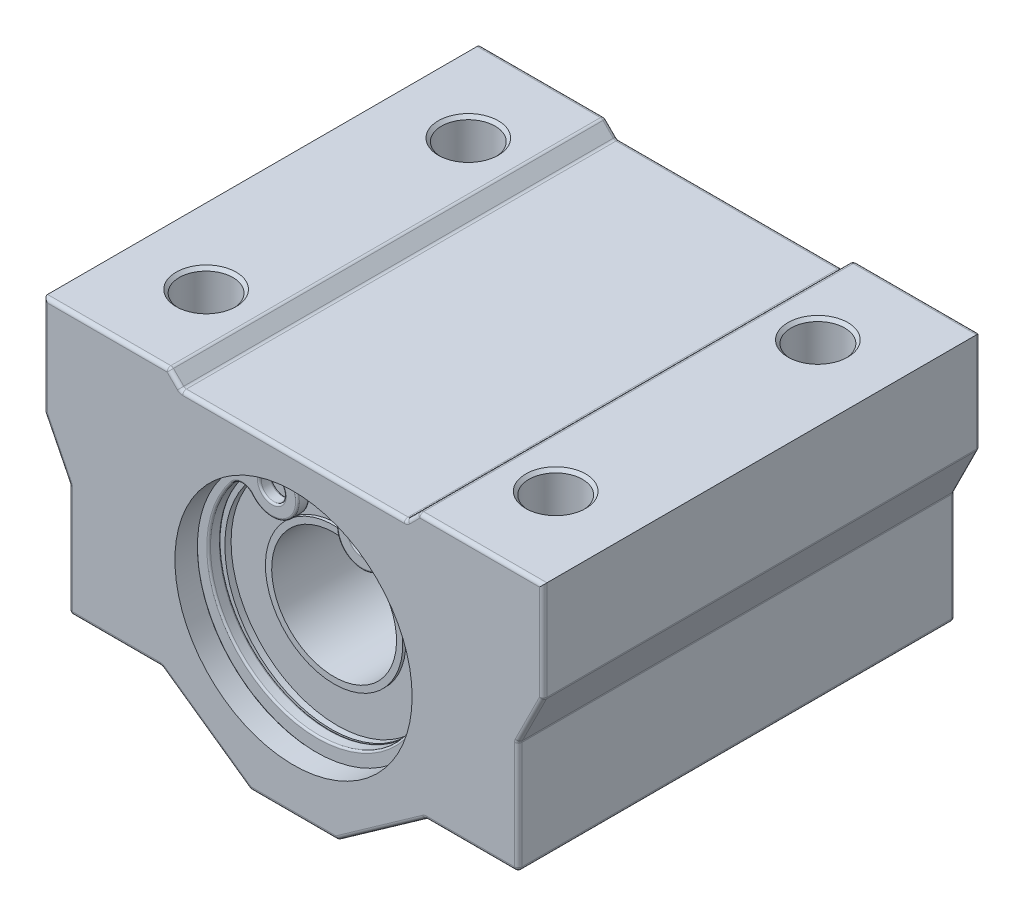
SolidWorks part; units mm, degrees
material "6061 Alloy"
ref_plane "Piano frontale" through (0, 0, 0) normal (0, 0, 1) x (1, 0, 0)
ref_plane "Piano superiore" through (0, 0, 0) normal (0, 1, 0) x (1, 0, 0)
ref_plane "Piano destro" through (0, 0, 0) normal (1, 0, 0) x (0, 0, -1)
sketch "Schizzo1" plane through (0, 0, 0) normal (0, 0, 1) x (1, 0, 0)
  line L0 (0, 25) -> (0, -25) construction
  line L1 (-30, 0) -> (30, 0) construction
  line L2 (3.5, -13) -> (10.5833, -8)
  line L3 (10.5833, -8) -> (18, -8)
  line L4 (18, -8) -> (18, 1)
  line L5 (18, 1) -> (20, 5)
  line L6 (20, 5) -> (20, 13)
  line L8 (20, 13) -> (10, 13)
  line L9 (9, 12) -> (10, 13)
  line L10 (-20, 12) -> (19, 12) construction
  line L15 (-3.5, -13) -> (-10.5833, -8)
  line L16 (-10.5833, -8) -> (-18, -8)
  line L17 (-18, -8) -> (-18, 1)
  line L18 (-18, 1) -> (-20, 5)
  line L19 (-20, 5) -> (-20, 13)
  line L20 (-20, 13) -> (-10, 13)
  line L24 (-9, 12) -> (-10, 13)
  line L26 (-9, 12) -> (9, 12)
  line L27 (-3.5, -13) -> (3.5, -13)
  circle A0 centre (0, 0) radius 9.5
  point P3 (0, 0)
  point P6 (0, 0)
  point P8 (0, -13)
  point P17 (0, 12)
  point P24 (19.5, 12.5)
  point P55 (0, -7.6504)
  dimension "D4" = 19
  dimension "D5" = 7
  dimension "D2" = 9
  dimension "D1" = 45
  dimension "D3" = 35.218
  dimension "D6" = 1
  dimension "D8" = 36
  dimension "G" = 21
  dimension "T" = 8
  dimension "F" = 26
  dimension "W" = 40
  dimension "E" = 20
  dimension "h" = 13
  dimension "L1" = 12
extrude "Estrusione-Estrusione1" add sketch "Schizzo1" along normal mid plane 35
hole_wizard "Foro per Vite M5-2" positions "Schizzo3" profile "Schizzo4" hole size "M5" standard "ISO" end condition through all
sketch "Schizzo3" plane through (0, 13, 0) normal (0, 1, 0) x (1, 0, 0)
  line L3 (0, 0) -> (-18, 0) construction
  line L5 (0, 0) -> (0, 17) construction
  line L6 (-20, -17.5) -> (-20, 17.5) construction
  line L7 (-10, 17.5) -> (-20, 17.5) construction
  point P0 (-14, 10.5)
  dimension "D1" = 14
  dimension "D2" = 10.5
  dimension "D3" = 6
  dimension "D4" = 7
sketch "Schizzo4" plane through (-14, 13, -10.5) normal (1, 0, 0) x (0, 0, 1)
  line L0 (0, 0) -> (0, 26)
  line L1 (0, 26) -> (2.15, 26)
  line L2 (2.15, 26) -> (2.15, 0)
  line L5 (2.15, 0) -> (0, 0)
  line L11 (0, -6.35) -> (0, 107.95) construction
  dimension "Thru Hole Dia." = 4.3
  dimension "Thru Hole Depth" = 26
pattern_linear "Ripetizione a L1" count 2 spacing 28 along (1, 0, 0) count 2 spacing 21 along (0, 0, 1) of "Foro per Vite M5-2"
chamfer "Smusso1" distance 0.25 angle 45 4 edges at (-14, 13, 12.65) (14, 13, 12.65) (14, 13, -8.35) (-14, 13, -8.35)
chamfer "Smusso2" distance 0.5 angle 45 4 edges at (14, -8, -8.35) (14, -8, 12.65) (-16.15, -8, 10.5) (-16.15, -8, -10.5)
sketch "Schizzo6" plane through (0, 0, 0) normal (1, 0, 0) x (0, 0, -1)
  line L0 (-20, 0) -> (20, 0) construction
  line L3 (-14.5, 8.5) -> (-14, 8.5)
  line L4 (-14, 8.5) -> (-14, 5.5)
  line L9 (14, 8.5) -> (14, 5.5)
  line L13 (-14.5, 9.5) -> (-14.5, 8.5)
  line L14 (0, -1.396) -> (0, 15.3751) construction
  line L15 (-14.5, 9.5) -> (14.5, 9.5)
  line L18 (14.5, 9.5) -> (14.5, 8.5)
  line L19 (14.5, 8.5) -> (14, 8.5)
  line L20 (-14, 5.5) -> (-14.25, 5.5)
  line L21 (14, 5.5) -> (14.25, 5.5)
  line L22 (-14.25, 5.5) -> (-14.25, 0)
  line L23 (14.25, 5.5) -> (14.25, 0)
  line L24 (14.25, 0) -> (-14.25, 0)
  point P3 (0, 0)
  point P7 (0, 9.5)
  dimension "D1" = 29
  dimension "D2" = 1
  dimension "D3" = 0.5
  dimension "D4" = 0.25
  dimension "D5" = 5.5
  dimension "D6" = 9.5
revolve "Rivoluzione1" add sketch "Schizzo6" angle 360 about L0
fillet "Raccordo1" radius 0.3 46 edges at (-10, 13, 0) (-9, 12, 0) (10, 13, 0) (9, 12, 0) (-20, 5, 0) (-18, 1, 0) (-18, -8, 0) (-10.5833, -8, 0) (20, 5, 0) (18, -8, 0) (18, 1, 0) (10.5833, -8, 0) (-3.5, -13, 0) (3.5, -13, 0) (-7.0417, -10.5, 17.5) (-14.2917, -8, 17.5) (-18, -3.5, 17.5) (-19, 3, 17.5) (-20, 9, 17.5) (-15, 13, 17.5) (-9.5, 12.5, 17.5) (0, 12, 17.5) (9.5, 12.5, 17.5) (15, 13, 17.5) (20, 9, 17.5) (19, 3, 17.5) (18, -3.5, 17.5) (14.2917, -8, 17.5) (7.0417, -10.5, 17.5) (0, -13, 17.5) (7.0417, -10.5, -17.5) (14.2917, -8, -17.5) (18, -3.5, -17.5) (19, 3, -17.5) (20, 9, -17.5) (15, 13, -17.5) (9.5, 12.5, -17.5) (0, 12, -17.5) (-9.5, 12.5, -17.5) (-15, 13, -17.5) (-20, 9, -17.5) (-19, 3, -17.5) (-18, -3.5, -17.5) (-14.2917, -8, -17.5) (-7.0417, -10.5, -17.5) (0, -13, -17.5)
sketch "Schizzo8" plane through (0, 0, 0) normal (0, 0, 1) x (1, 0, 0)
  circle A0 centre (0, 0) radius 5
  dimension "D1" = 10
extrude "Taglio-Estrusione2" cut sketch "Schizzo8" against normal through all both and the other way through all
sketch "Schizzo7" plane through (0, 0, 0) normal (0, 0, 1) x (1, 0, 0)
  circle A0 centre (0, 0) radius 10
  dimension "D1" = 20
extrude "Taglio-Estrusione1" cut sketch "Schizzo7" along normal blind 1.1 from offset 14.6
mirror "Specchia1" about plane through (0, 0, 0) normal (0, 0, 1) of "Taglio-Estrusione1"
sketch "Schizzo9" plane through (0, 0, 0) normal (0, 0, 1) x (1, 0, 0)
  line L0 (-2.0925, 0) -> (2.1999, 0) construction
  line L1 (0, 22.577) -> (0, -2.423) construction
  line L2 (0, 0) -> (10.9663, 21.9949) construction
  line L3 (0, 0) -> (-11.179, 22.4215) construction
  arc A0 (-3.9648, 8.9075) -> (4.0283, 8.8789) centre (0, 0) ccw
  circle A2 centre (-3.6325, 6.9465) radius 1
  circle A3 centre (3.5909, 6.9185) radius 1
  arc A4 (-5.2379, 5.6717) -> (-3.4873, 8.9914) centre (-3.6325, 6.9465) ccw
  arc A5 (3.6382, 8.968) -> (5.2175, 5.6709) centre (3.5909, 6.9185) ccw
  arc A6 (-6.8029, 5.6731) -> (6.7917, 5.6872) centre (0, 0.25) ccw
  arc A7 (3.6382, 8.968) -> (4.0283, 8.8789) centre (3.6151, 7.9683) cw
  arc A8 (-3.9648, 8.9075) -> (-3.4873, 8.9914) centre (-3.5581, 7.9939) cw
  arc A9 (5.2175, 5.6709) -> (6.7917, 5.6872) centre (6.011, 5.0623) cw
  arc A10 (-5.2379, 5.6717) -> (-6.8029, 5.6731) centre (-6.021, 5.0498) ccw
  dimension "D1" = 19.5
  dimension "D3" = 0.25
  dimension "D6" = 2.05
  dimension "D5" = 8.7
  dimension "D7" = 2
  dimension "D4" = 53
  dimension "D8" = 26.5
extrude "Estrusione-Estrusione2" add sketch "Schizzo9" along normal blind 1 from offset 14.6 separate body
pattern_linear "Ripetizione a L2" count 2 spacing 30.2 along (0, 0, -1) of "Estrusione-Estrusione2"
fillet "Raccordo4" radius 0.15 20 edges at (4.5909, 6.9185, 15.6) (-2.6325, 6.9465, 14.6) (-2.6325, 6.9465, 15.6) (3.8377, 8.9432, 14.6) (1.7421, 6.0329, 14.6) (6.0006, 6.0622, 14.6) (-6.0201, 6.0498, 14.6) (-1.8192, 5.9903, 14.6) (-3.7312, 8.9788, 14.6) (-0.0348, -9.7499, 14.6) (3.8377, 8.9432, 15.6) (1.7421, 6.0329, 15.6) (6.0006, 6.0622, 15.6) (-6.0201, 6.0498, 15.6) (-1.8192, 5.9903, 15.6) (-3.7312, 8.9788, 15.6) (-0.0348, -9.7499, 15.6) (4.5909, 6.9185, 14.6) (0.009, -8.45, 14.6) (0.009, -8.45, 15.6)
fillet "Raccordo5" radius 0.15 20 edges at (4.5909, 6.9185, -14.6) (-2.6325, 6.9465, -14.6) (-0.0348, -9.7499, -14.6) (-3.7312, 8.9788, -14.6) (-1.8192, 5.9903, -14.6) (-6.0201, 6.0498, -14.6) (0.009, -8.45, -14.6) (6.0006, 6.0622, -14.6) (1.7421, 6.0329, -14.6) (3.8377, 8.9432, -14.6) (4.5909, 6.9185, -15.6) (1.7421, 6.0329, -15.6) (6.0006, 6.0622, -15.6) (0.009, -8.45, -15.6) (-6.0201, 6.0498, -15.6) (-1.8192, 5.9903, -15.6) (-3.7312, 8.9788, -15.6) (-0.0348, -9.7499, -15.6) (3.8377, 8.9432, -15.6) (-2.6325, 6.9465, -15.6)
